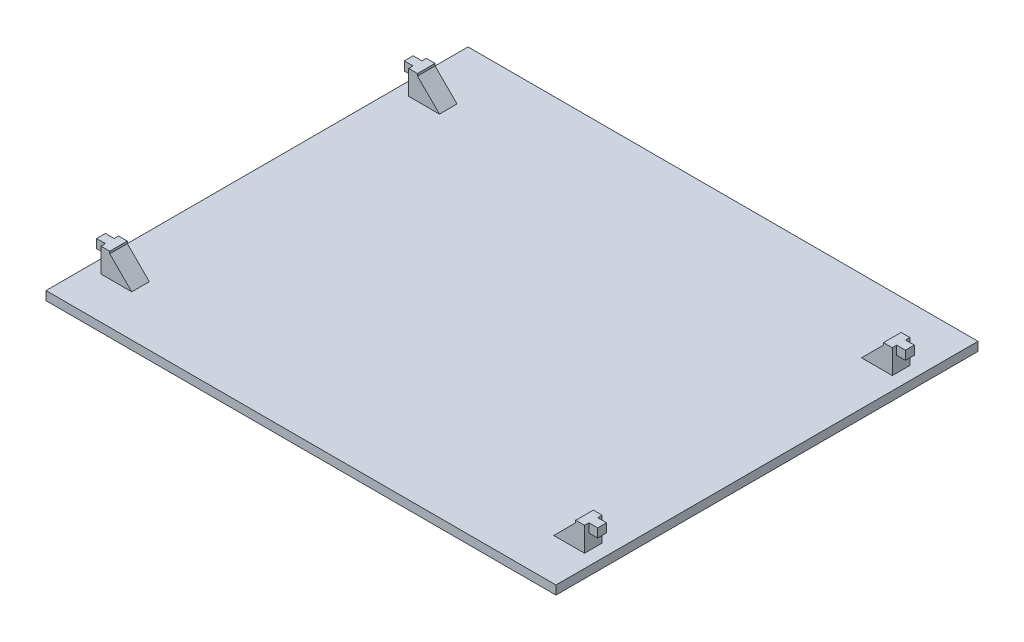
SolidWorks part; units mm, degrees
ref_plane "Front Plane" through (0, 0, 0) normal (0, 0, 1) x (1, 0, 0)
ref_plane "Top Plane" through (0, 0, 0) normal (0, 1, 0) x (1, 0, 0)
ref_plane "Right Plane" through (0, 0, 0) normal (1, 0, 0) x (0, 0, -1)
sketch "Sketch1" plane through (0, 0, 0) normal (0, 1, 0) x (1, 0, 0)
  line L1 (-58, 48) -> (58, 48)
  line L2 (-58, 48) -> (-58, -48)
  line L3 (-58, -48) -> (58, -48)
  line L4 (58, 48) -> (58, -48)
  line L5 (-58, 48) -> (58, -48) construction
  line L6 (-58, -48) -> (58, 48) construction
  point P0 (0, 0)
  dimension "D1" = 96
  dimension "D2" = 116
extrude "Boss-Extrude1" add sketch "Sketch1" along normal blind 2
sketch "Sketch2" plane through (0, 2, 0) normal (0, 1, 0) x (1, 0, 0)
  line L0 (0, 46.2627) -> (0, -47.1244) construction
  line L1 (58, -48) -> (58, 48) construction
  line L2 (53, -34.5) -> (55, -34.5)
  line L3 (53, -34.5) -> (53, -38.5)
  line L4 (53, -38.5) -> (55, -38.5)
  line L5 (55, -34.5) -> (55, -38.5)
  line L6 (0, 0) -> (76.1121, 0) construction
  line L7 (53, 35.5) -> (53, 31.5)
  line L8 (53, 35.5) -> (55, 35.5)
  line L9 (55, 35.5) -> (55, 31.5)
  line L10 (53, 31.5) -> (55, 31.5)
  dimension "D1" = 3
  dimension "D2" = 34.5
  dimension "D3" = 2
  dimension "D4" = 4
  dimension "D5" = 2
extrude "Boss-Extrude2" add sketch "Sketch2" along normal blind 5.5
sketch "Sketch3" plane through (55, 0, 0) normal (1, 0, 0) x (0, 0, -1)
  line L0 (-38.5, 7.5) -> (-34.5, 7.5) construction
  line L1 (-37.5, 7.5) -> (-35.5, 7.5)
  line L2 (-37.5, 7.5) -> (-37.5, 5.5)
  line L3 (-37.5, 5.5) -> (-35.5, 5.5)
  line L4 (-35.5, 7.5) -> (-35.5, 5.5)
  line L5 (0, 0) -> (0, 23.6371) construction
  line L6 (32.5, 7.5) -> (32.5, 5.5)
  line L7 (32.5, 7.5) -> (34.5, 7.5)
  line L8 (34.5, 7.5) -> (34.5, 5.5)
  line L9 (32.5, 5.5) -> (34.5, 5.5)
  line L10 (70, 0) -> (70, 23.6371) construction
  point P6 (-36.5, 7.5)
  point P7 (-36.5, 7.5)
  dimension "D1" = 2
  dimension "D2" = 2
  dimension "D3" = 2
extrude "Boss-Extrude3" add sketch "Sketch3" along normal blind 2
mirror "Mirror1" about plane through (0, 0, 0) normal (1, 0, 0) of "Boss-Extrude3", "Boss-Extrude2"
ref_plane "Plane5" through (53, 2, -35.5) normal (0, 0, 1) x (1, 0, 0)
chamfer "Chamfer2" distance 5 angle 45 4 edges at (-53, 2, 36.5) (-53, 2, -33.5) (53, 2, -33.5) (53, 2, 36.5)
